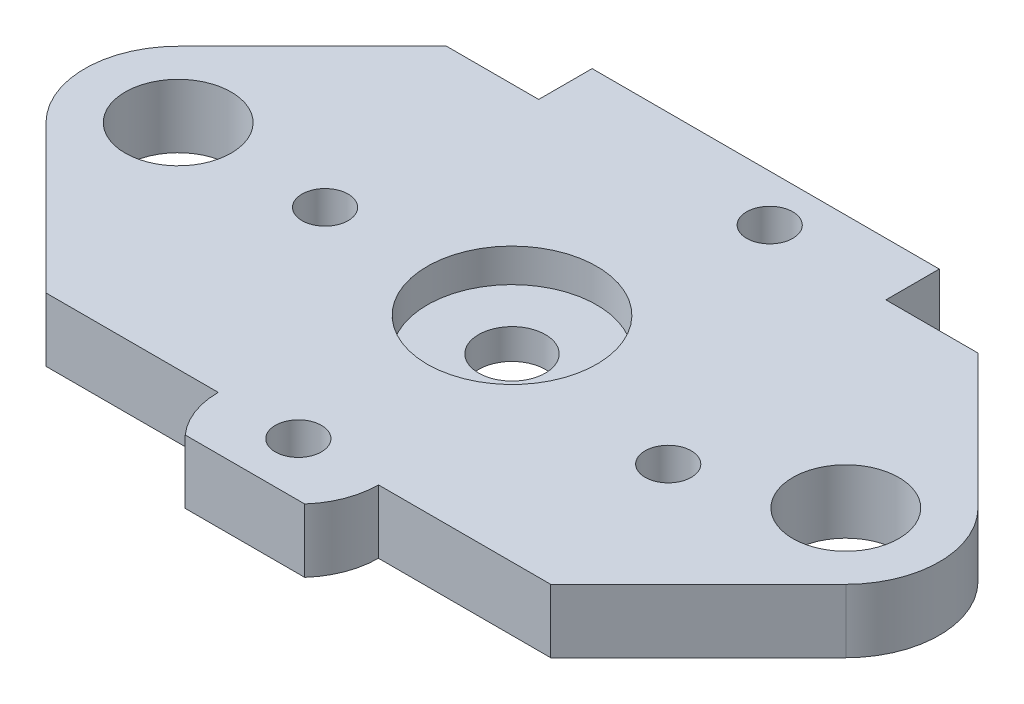
SolidWorks part; units mm, degrees
material "6061 Alloy"
ref_plane "Front Plane" through (0, 0, 0) normal (0, 0, 1) x (1, 0, 0)
ref_plane "Top Plane" through (0, 0, 0) normal (0, 1, 0) x (1, 0, 0)
ref_plane "Right Plane" through (0, 0, 0) normal (1, 0, 0) x (0, 0, -1)
sketch "Sketch1" plane through (0, 0, 0) normal (0, 1, 0) x (1, 0, 0)
  line L0 (-32.5, -22.5) -> (32.5, 22.5) construction
  line L1 (-32.5, 22.5) -> (32.5, 22.5)
  line L2 (-32.5, 22.5) -> (-32.5, -22.5)
  line L3 (-32.5, -22.5) -> (32.5, -22.5)
  line L4 (32.5, 22.5) -> (32.5, -22.5)
  dimension "D1" = 45
  dimension "D2" = 65
extrude "Boss-Extrude1" add sketch "Sketch1" along normal blind 4.7625
sketch "Sketch2" plane through (0, 4.7625, 0) normal (0, 1, 0) x (1, 0, 0)
  circle A0 centre (0, 0) radius 2.5
  dimension "D1" = 5
extrude "Cut-Extrude1" cut sketch "Sketch2" against normal through all
hole_wizard "#8-32 Tapped Hole1" positions "Sketch5" profile "Sketch4" tap size "#8-32" standard "Ansi Inch" end condition through all
sketch "Sketch5" plane through (-15.7609, 4.7625, 28.4272) normal (0, 1, 0) x (-1, 0, 0)
  circle A1 centre (-15.7609, -28.4272) radius 2.5 construction
  point P0 (-31.2609, -24.6272)
  point P1 (-1.7609, -28.4272)
  point P3 (-19.5609, -43.9272)
  point P12 (-15.7609, -12.4272)
  dimension "D1" = 3.8
  dimension "D2" = 15.5
  dimension "D4" = 16
  dimension "D5" = 15.5
  dimension "D6" = 14
  dimension "D7" = 3.8
sketch "Sketch4" plane through (15.5, 4.7625, 3.8) normal (1, 0, 0) x (0, 0, 1)
  line L0 (0, 0) -> (0, 4.7625)
  line L1 (0, 4.7625) -> (1.7272, 4.7625)
  line L2 (1.7272, 4.7625) -> (1.7272, 0)
  line L5 (1.7272, 0) -> (0, 0)
  line L11 (0, -6.35) -> (0, 107.95) construction
  dimension "Thru Tap Drill Dia." = 3.4544
  dimension "Thru Tap Drill Depth" = 4.7625
cosmetic thread "Hole Thread1" parameters "D2"=4.1656
cosmetic thread "Hole Thread4" parameters "D2"=4.1656
cosmetic thread "Hole Thread5" parameters "D2"=4.1656
cosmetic thread "Hole Thread6" parameters "D2"=4.1656
sketch "Sketch6" plane through (0, 4.7625, 0) normal (0, 1, 0) x (1, 0, 0)
  line L0 (-25, 0) -> (25, 0) construction
  circle A0 centre (-25, 0) radius 3.9688
  circle A1 centre (25, 0) radius 3.9688
  dimension "D1" = 7.9375
  dimension "D2" = 50
extrude "Cut-Extrude2" cut sketch "Sketch6" against normal through all
sketch "Sketch8" plane through (0, 4.7625, 0) normal (0, 1, 0) x (1, 0, 0)
  line L0 (6, -16) -> (18.8995, -16)
  line L1 (18.8995, -16) -> (29.9497, -4.9497)
  line L2 (29.9497, 4.9497) -> (19.8995, 15)
  line L3 (32.5, 22.5) -> (-32.5, 22.5) construction
  line L4 (0, 22.5) -> (32.5, 22.5)
  line L5 (32.5, 22.5) -> (32.5, -22.5)
  line L6 (32.5, -22.5) -> (0, -22.5)
  line L7 (-32.5, -22.5) -> (32.5, -22.5) construction
  line L8 (0, -22.5) -> (0, -20)
  line L9 (4.4721, -20) -> (0, -20)
  line L10 (13, 19) -> (0, 19)
  line L11 (0, 19) -> (0, 22.5)
  line L14 (13, 19) -> (13, 15)
  line L15 (13, 15) -> (19.8995, 15)
  arc A0 (4.4721, -20) -> (6, -16) centre (0, -16) ccw
  arc A1 (29.9497, -4.9497) -> (29.9497, 4.9497) centre (25, 0) ccw
  circle A2 centre (25, 0) radius 3.9688 construction
  dimension "D1" = 12
  dimension "D2" = 14
  dimension "D3" = 45
  dimension "D4" = 2.5
  dimension "D5" = 3.5
  dimension "D6" = 13
  dimension "D7" = 15
extrude "Cut-Extrude3" cut sketch "Sketch8" against normal through all
mirror "Mirror1" about plane through (0, 0, 0) normal (1, 0, 0) of "Cut-Extrude3"
sketch "Sketch9" plane through (0, 4.7625, 0) normal (0, 1, 0) x (1, 0, 0)
  circle A0 centre (0, 0) radius 6.35
  dimension "D1" = 12.7
extrude "Cut-Extrude4" cut sketch "Sketch9" against normal blind 2.5
